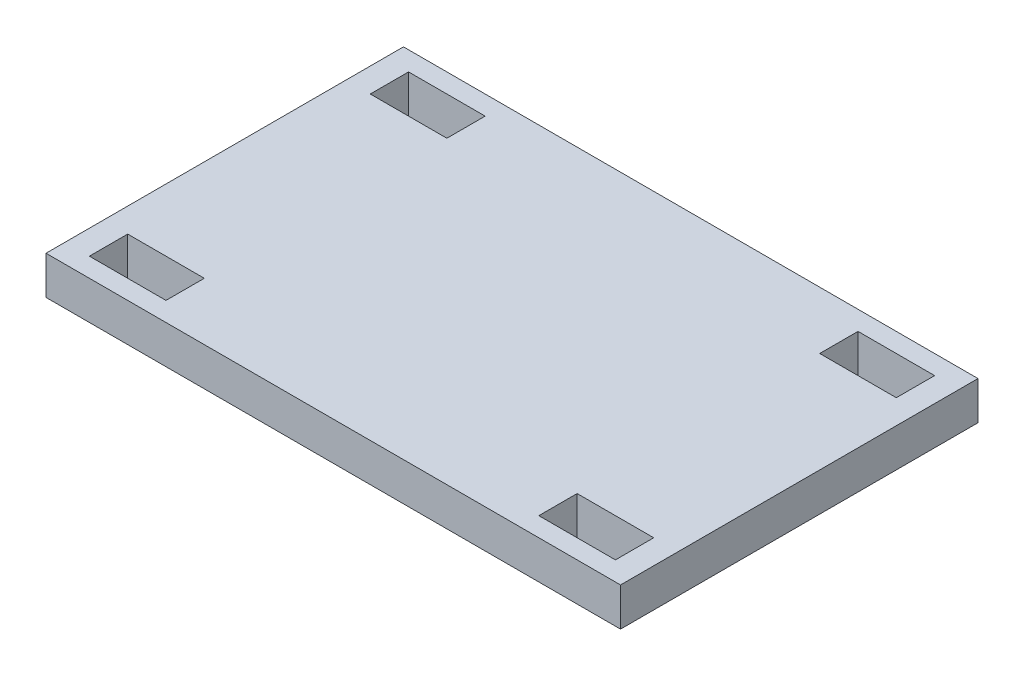
SolidWorks part; units mm, degrees
ref_plane "정면" through (0, 0, 0) normal (0, 0, 1) x (1, 0, 0)
ref_plane "윗면" through (0, 0, 0) normal (0, 1, 0) x (1, 0, 0)
ref_plane "우측면" through (0, 0, 0) normal (1, 0, 0) x (0, 0, -1)
sketch "스케치1" plane through (0, 0, 0) normal (0, 1, 0) x (1, 0, 0)
  line L1 (0, 0) -> (45, 0)
  line L2 (0, 0) -> (0, 28)
  line L3 (0, 28) -> (45, 28)
  line L4 (45, 0) -> (45, 28)
  dimension "D1" = 28
  dimension "D2" = 45
extrude "보스-돌출1" add sketch "스케치1" along normal blind 3
sketch "스케치2" plane through (0, 3, 0) normal (0, 1, 0) x (1, 0, 0)
  line L0 (0, 28) -> (0, 0) construction
  line L1 (22.5, 28.6714) -> (22.5, -1.6267) construction
  line L2 (-9.7081, 14) -> (48.4952, 14) construction
  line L3 (1.8986, 26.5) -> (7.8986, 26.5)
  line L4 (1.8986, 26.5) -> (1.8986, 23.5)
  line L5 (1.8986, 23.5) -> (7.8986, 23.5)
  line L6 (7.8986, 26.5) -> (7.8986, 23.5)
  line L7 (1.8986, 4.5) -> (7.8986, 4.5)
  line L8 (1.8986, 1.5) -> (1.8986, 4.5)
  line L9 (1.8986, 1.5) -> (7.8986, 1.5)
  line L10 (7.8986, 1.5) -> (7.8986, 4.5)
  line L11 (43.1014, 1.5) -> (43.1014, 4.5)
  line L12 (43.1014, 1.5) -> (37.1014, 1.5)
  line L13 (37.1014, 1.5) -> (37.1014, 4.5)
  line L14 (43.1014, 4.5) -> (37.1014, 4.5)
  line L15 (43.1014, 23.5) -> (37.1014, 23.5)
  line L16 (37.1014, 26.5) -> (37.1014, 23.5)
  line L17 (43.1014, 26.5) -> (37.1014, 26.5)
  line L18 (43.1014, 26.5) -> (43.1014, 23.5)
  point P0 (0, 25)
  point P1 (0, 14)
  point P6 (0, 3)
  dimension "D1" = 11
  dimension "D2" = 11
  dimension "D3" = 1.5
  dimension "D4" = 1.5
  dimension "D5" = 6
extrude "컷-돌출1" cut sketch "스케치2" against normal through all
